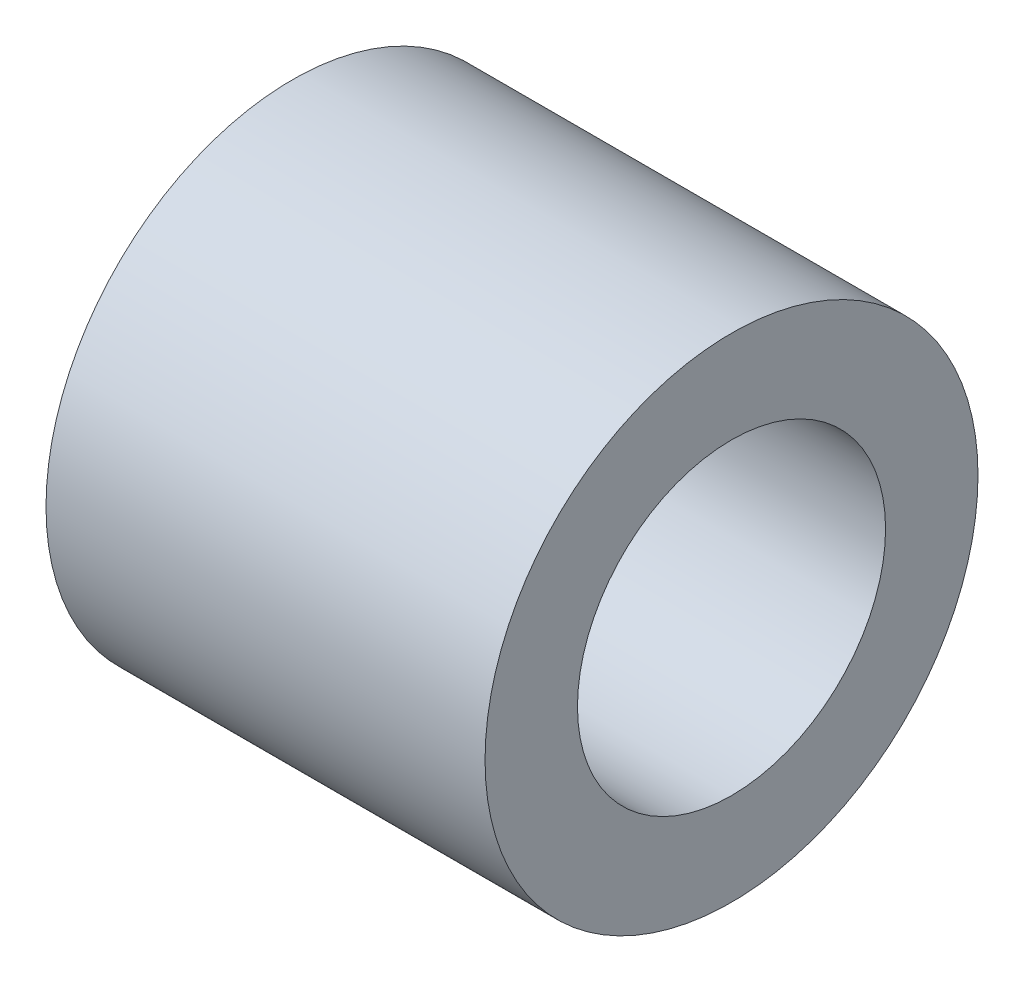
SolidWorks part; units mm, degrees
ref_plane "Face" through (0, 0, 0) normal (0, 0, 1) x (1, 0, 0)
ref_plane "Dessus" through (0, 0, 0) normal (0, 1, 0) x (1, 0, 0)
ref_plane "Droite" through (0, 0, 0) normal (1, 0, 0) x (0, 0, -1)
sketch "Esquisse1" plane through (0, 0, 0) normal (0, 0, 1) x (1, 0, 0)
  line L0 (0, 0) -> (61.8738, 0) construction
  line L1 (0, 0) -> (0, 11.5949) construction
  line L2 (1, 1) -> (3.85, 1)
  line L3 (1, 1) -> (1, 1.6)
  line L4 (1, 1.6) -> (3.85, 1.6)
  line L5 (3.85, 1) -> (3.85, 1.6)
  dimension "D1" = 2
  dimension "D2" = 3.2
  dimension "D3" = 2.85
  dimension "D4" = 1
revolve "Révolution1" add sketch "Esquisse1" angle 360 about L0
sketch "Esquisse3" plane through (3.85, 0, 0) normal (1, 0, 0) x (0, 0, -1)
  line L0 (0, -5.3958) -> (0, 6.4021) construction
  line L2 (0.5, 3.0761) -> (3.1004, 3.0761)
  line L3 (0.5, 3.0761) -> (0.5, -3.3504)
  line L4 (0.5, -3.3504) -> (3.1004, -3.3504)
  line L5 (3.1004, 3.0761) -> (3.1004, -3.3504)
  dimension "D1" = 0.5
extrude "Enlèv. mat.-Extru.1" [suppressed] cut sketch "Esquisse3" against normal through all
